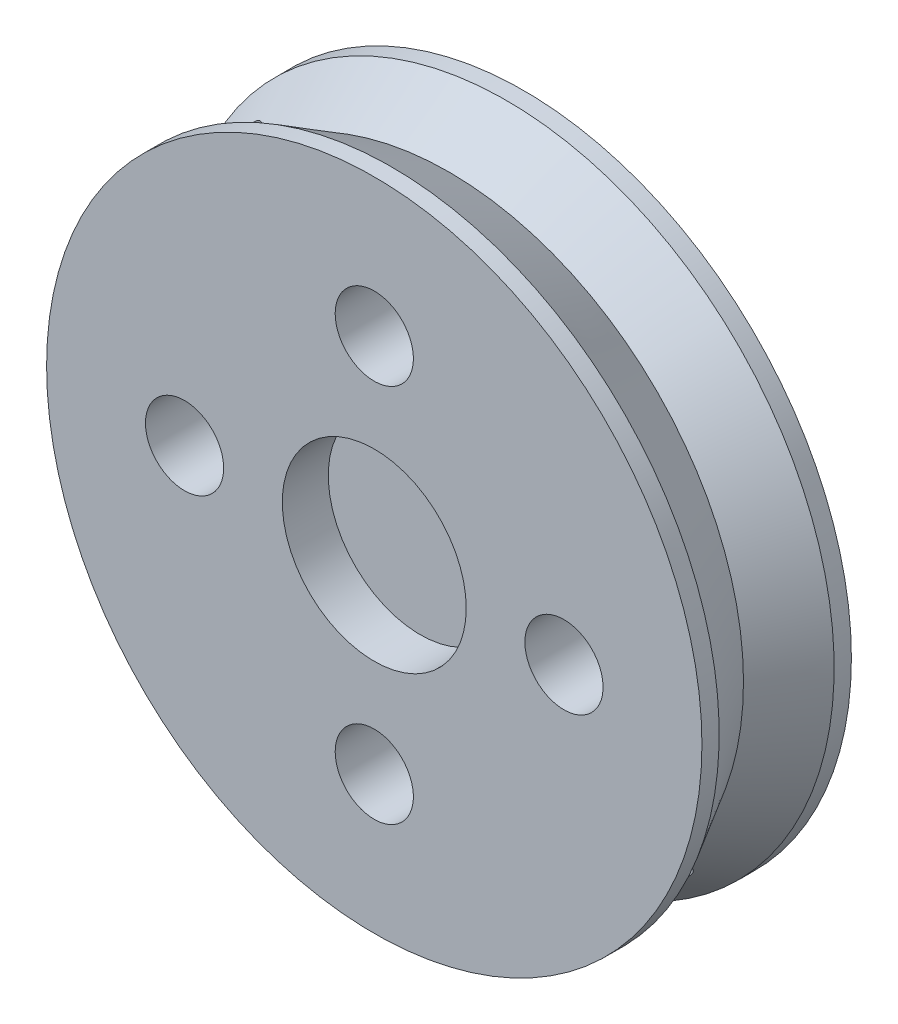
SolidWorks part; units mm, degrees
ref_plane "Plan de face" through (0, 0, 0) normal (0, 0, 1) x (1, 0, 0)
ref_plane "Plan de dessus" through (0, 0, 0) normal (0, 1, 0) x (1, 0, 0)
ref_plane "Plan de droite" through (0, 0, 0) normal (1, 0, 0) x (0, 0, -1)
sketch "Esquisse2" plane through (0, 0, 0) normal (0, 0, 1) x (1, 0, 0)
  circle A0 centre (0, 0) radius 14.25
  circle A1 centre (0, 0) radius 8.25
  dimension "D1" = 28.5
  dimension "D2" = 16.5
extrude "Boss.-Extru.1" add sketch "Esquisse2" along normal mid plane 6.5 contours A0
sketch "Esquisse3" plane through (0, 0, 0) normal (0, 0, 1) x (1, 0, 0)
  circle A2 centre (0, 8.25) radius 1.2
  circle A3 centre (-8.25, 0) radius 1.2
  circle A4 centre (0, -8.25) radius 1.2
  circle A5 centre (8.25, 0) radius 1.2
  point P3 (-8.25, 0)
  point P11 (0, 8.25)
  point P12 (8.25, 0)
  point P13 (0, -8.25)
  dimension "D1" = 2.4
  dimension "D2" = 2.4
  dimension "D3" = 2.4
  dimension "D4" = 2.4
extrude "Enlèv. mat.-Extru.1" cut sketch "Esquisse3" along normal through all
sketch "Esquisse10" plane through (0, 0, -3.25) normal (0, 0, -1) x (-1, 0, 0)
  circle A0 centre (-8.25, 0) radius 1.7
  circle A1 centre (0, 8.25) radius 1.7
  circle A2 centre (8.25, 0) radius 1.7
  circle A3 centre (0, -8.25) radius 1.7
  dimension "D1" = 3.4
  dimension "D2" = 3.4
  dimension "D3" = 3.4
  dimension "D4" = 3.4
extrude "Enlèv. mat.-Extru.2" cut sketch "Esquisse10" against normal through all and the other way through all
sketch "Esquisse11" plane through (0, 0, -3.25) normal (0, 0, -1) x (-1, 0, 0)
  line L0 (0, 0) -> (0, -14.25)
  line L1 (0, -14.25) -> (0, 0)
  line L2 (-14.25, 0) -> (0, 0)
  line L3 (0, 0) -> (-10.0763, -10.0763)
  line L4 (-10.0763, -10.0763) -> (10.0763, 10.0763)
  line L5 (-10.0763, -10.0763) -> (-13.3052, -6.8474)
  line L6 (-13.3052, -6.8474) -> (-7.1266, -13.0259)
  circle A0 centre (0, 0) radius 14.25 construction
ref_plane "Plan1" through (10.0763, -10.0763, 0) normal (0.7071, -0.7071, 0) x (-0.7071, -0.7071, 0)
sketch "Esquisse13" plane through (10.0763, -10.0763, 0) normal (0.7071, -0.7071, 0) x (-0.7071, -0.7071, 0)
  line L0 (0, 0) -> (0, -3.25)
  line L1 (-14.25, -3.25) -> (14.25, -3.25) construction
  circle A1 centre (0, 0) radius 1
  dimension "D2" = 2
sketch "Esquisse16" plane through (0, 0, 3.25) normal (0, 0, 1) x (1, 0, 0)
  line L0 (0, 0) -> (-6.1179, -5.0018)
sketch "Esquisse17" plane through (0, 0, 3.25) normal (0, 0, 1) x (1, 0, 0)
  circle A0 centre (0, 0) radius 4
  dimension "D1" = 8
extrude "Enlèv. mat.-Extru.8" cut sketch "Esquisse17" against normal blind 2
sketch "Esquisse14" plane through (0, 0, 0) normal (0, 0, 1) x (1, 0, 0)
  circle A0 centre (0, 0) radius 11.75
  circle A1 centre (0, 0) radius 14.25
  dimension "D1" = 23.5
extrude "Enlèv. mat.-Extru.4" cut sketch "Esquisse13" against normal through all contours A1
sketch "Esquisse18" plane through (0, 0, 0) normal (0, 1, 0) x (1, 0, 0)
  line L0 (14.25, 2.5) -> (12.8066, 0)
  line L1 (14.25, -3.25) -> (14.25, 3.25) construction
  line L2 (12.8066, 0) -> (14.25, -2.5)
  line L3 (14.25, -2.5) -> (14.25, 2.5)
  line L4 (-14.25, 0) -> (14.25, 0) construction
  line L5 (12.8066, 0) -> (14.25, 0) construction
  point P4 (14.25, 0)
  point P10 (12.8066, 0)
  dimension "D1" = 30
  dimension "D2" = 30
  dimension "D3" = 5
  dimension "D4" = 1.4434
sketch "Esquisse19" plane through (0, 0, 0) normal (1, 0, 0) x (0, 0, -1)
  line L0 (3.25, 0) -> (-5.3209, 0) construction
revolve "Enlèvement de matière-Révolution1" cut sketch "Esquisse18" angle 360 about L0
ref_plane "Plan2" through (9.7351, -8.3209, 0) normal (-0.6497, -0.7602, 0) x (-0.7602, 0.6497, 0)
